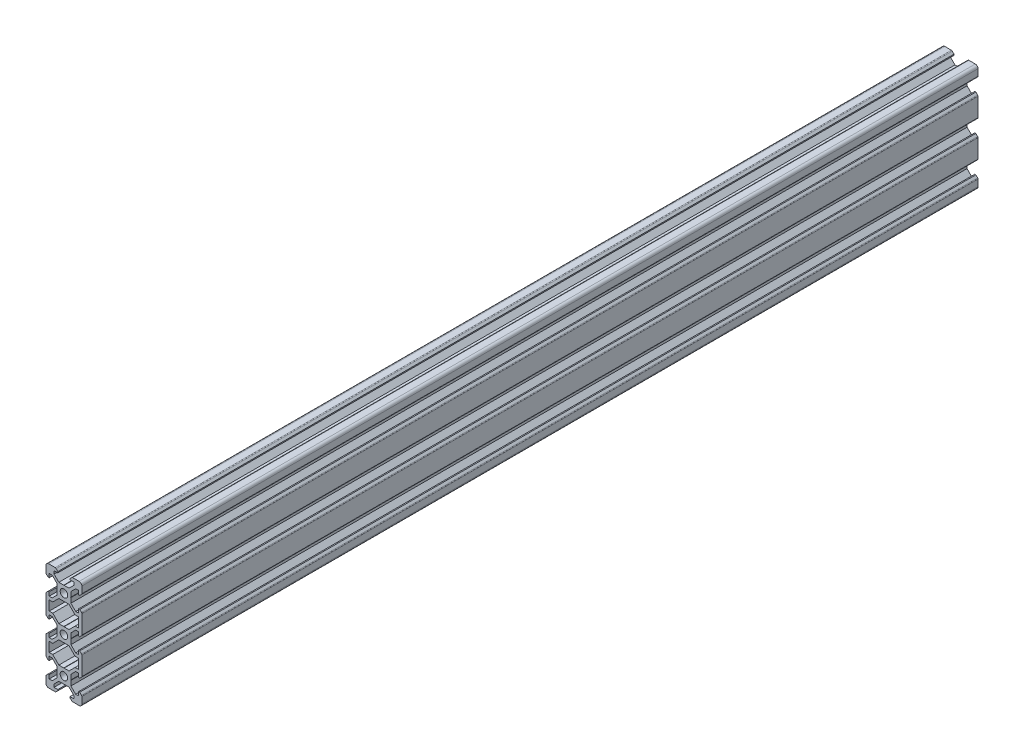
SolidWorks part; units mm, degrees
material "6063-T5"
ref_plane "Front" through (0, 0, 0) normal (0, 0, 1) x (1, 0, 0)
ref_plane "Top" through (0, 0, 0) normal (0, 1, 0) x (1, 0, 0)
ref_plane "Right" through (0, 0, 0) normal (1, 0, 0) x (0, 0, -1)
sketch "Sketch1" plane through (0, 0, 0) normal (0, 0, 1) x (1, 0, 0)
  line L0 (-8.5, 10) -> (-10, 8.5) construction
  line L1 (-8.5, 10) -> (-4.8628, 10)
  line L2 (-10, 8.5) -> (-10, 4.8628)
  line L3 (25.9287, -20) -> (-28.3599, -20) construction
  line L4 (10, 8.5) -> (10, 4.8628)
  line L5 (-10, 10) -> (10, -10) construction
  line L6 (-10, -10) -> (10, 10) construction
  line L7 (8.2, -5.5) -> (8.2, -3.3865)
  line L8 (-8.2, -5.5) -> (-8.2, -3.3865)
  line L9 (-5.5, 8.2) -> (-3.3865, 8.2)
  line L10 (-8.2, -12.7) -> (-8.2, -7.3)
  line L11 (-3.9005, 2.8395) -> (-6.561, 5.5)
  line L12 (-6.561, 5.5) -> (-8.2, 5.5)
  line L13 (-2.8395, -3.9005) -> (-0.1, -3.9005)
  line L14 (-3.9005, -2.8395) -> (-3.9005, -0.1)
  line L15 (-2.8395, 3.9005) -> (-0.1, 3.9005)
  line L16 (3.9005, -2.8395) -> (3.9005, -0.1)
  line L17 (-8.2, 3.3865) -> (-8.81, 3.3865)
  line L18 (-8.81, 3.3865) -> (-9.7976, 4.3741)
  line L19 (8.5, 10) -> (10, 8.5) construction
  line L20 (-2.8395, 3.9005) -> (-5.5, 6.561)
  line L21 (-5.5, 6.561) -> (-5.5, 8.2)
  line L22 (-3.3865, 8.2) -> (-3.3865, 8.81)
  line L23 (-3.3865, 8.81) -> (-4.3741, 9.7976)
  line L24 (0, 24.069) -> (0, -33.8154) construction
  line L25 (3.3865, 8.81) -> (4.3741, 9.7976)
  line L26 (3.3865, 8.2) -> (3.3865, 8.81)
  line L27 (5.5, 6.561) -> (5.5, 8.2)
  line L28 (2.8395, 3.9005) -> (5.5, 6.561)
  line L29 (3.3865, 8.2) -> (5.5, 8.2)
  line L30 (4.8628, 10) -> (8.5, 10)
  line L31 (-0.1, 3.9005) -> (0, 3.8005)
  line L32 (0.1, 3.9005) -> (0, 3.8005)
  line L33 (0.1, 3.9005) -> (2.8395, 3.9005)
  line L34 (25.9287, 0) -> (-28.3459, 0) construction
  line L35 (-0.1, -3.9005) -> (0, -3.8005)
  line L36 (0.1, -3.9005) -> (0, -3.8005)
  line L37 (0.1, -3.9005) -> (2.8395, -3.9005)
  line L38 (-3.9005, 0.1) -> (-3.8005, 0)
  line L39 (-3.8005, 0) -> (-3.9005, -0.1)
  line L40 (-3.9005, 0.1) -> (-3.9005, 2.8395)
  line L41 (3.9005, 0.1) -> (3.8005, 0)
  line L42 (3.8005, 0) -> (3.9005, -0.1)
  line L43 (3.9005, 0.1) -> (3.9005, 2.8395)
  line L44 (8.81, 3.3865) -> (9.7976, 4.3741)
  line L45 (8.2, 3.3865) -> (8.81, 3.3865)
  line L46 (6.561, 5.5) -> (8.2, 5.5)
  line L47 (3.9005, 2.8395) -> (6.561, 5.5)
  line L48 (2.8395, -3.9005) -> (5.5, -6.561)
  line L49 (3.9005, -2.8395) -> (6.561, -5.5)
  line L50 (-2.8395, -3.9005) -> (-5.5, -6.561)
  line L51 (-3.9005, -2.8395) -> (-6.561, -5.5)
  line L52 (6.561, -5.5) -> (8.2, -5.5)
  line L53 (-6.561, -5.5) -> (-8.2, -5.5)
  line L54 (-8.81, -3.3865) -> (-9.7976, -4.3741)
  line L55 (-8.2, -3.3865) -> (-8.81, -3.3865)
  line L56 (8.81, -3.3865) -> (9.7976, -4.3741)
  line L57 (8.2, -3.3865) -> (8.81, -3.3865)
  line L58 (8.2, 3.3865) -> (8.2, 5.5)
  line L59 (10, -4.8628) -> (10, -15.1372)
  line L60 (-8.2, 3.3865) -> (-8.2, 5.5)
  line L61 (-10, -4.8628) -> (-10, -15.1372)
  line L62 (-28.3459, -10) -> (-10, -10) construction
  line L63 (-3.9005, -20.1) -> (-3.9005, -22.8395)
  line L64 (-3.9005, -20.1) -> (-3.8005, -20)
  line L65 (-3.8005, -20) -> (-3.9005, -19.9)
  line L66 (3.9005, -20.1) -> (3.9005, -22.8395)
  line L67 (3.9005, -20.1) -> (3.8005, -20)
  line L68 (3.8005, -20) -> (3.9005, -19.9)
  line L69 (6.561, -14.5) -> (8.2, -14.5)
  line L70 (3.9005, -17.1605) -> (6.561, -14.5)
  line L71 (3.9005, -17.1605) -> (3.9005, -19.9)
  line L72 (-3.9005, -17.1605) -> (-3.9005, -19.9)
  line L73 (-3.9005, -17.1605) -> (-6.561, -14.5)
  line L74 (-6.561, -14.5) -> (-8.2, -14.5)
  line L75 (-8.2, -16.6135) -> (-8.81, -16.6135)
  line L76 (-8.81, -16.6135) -> (-9.7976, -15.6259)
  line L77 (8.2, -16.6135) -> (8.81, -16.6135)
  line L78 (8.81, -16.6135) -> (9.7976, -15.6259)
  line L79 (-2.8395, -16.0995) -> (-5.5, -13.439)
  line L80 (-2.8395, -16.0995) -> (-0.1, -16.0995)
  line L81 (-0.1, -16.0995) -> (0, -16.1995)
  line L82 (0.1, -16.0995) -> (0, -16.1995)
  line L83 (0.1, -16.0995) -> (2.8395, -16.0995)
  line L84 (2.8395, -16.0995) -> (5.5, -13.439)
  line L85 (-8.2, -16.6135) -> (-8.2, -14.5)
  line L86 (8.2, -16.6135) -> (8.2, -14.5)
  line L87 (2.8395, -23.9005) -> (5.5, -26.561)
  line L88 (-2.8395, -23.9005) -> (-5.5, -26.561)
  line L89 (-0.1, -23.9005) -> (0, -23.8005)
  line L90 (0.1, -23.9005) -> (0, -23.8005)
  line L91 (0.1, -23.9005) -> (2.8395, -23.9005)
  line L92 (-2.8395, -23.9005) -> (-0.1, -23.9005)
  line L93 (-8.2, -23.3865) -> (-8.2, -25.5)
  line L94 (-8.2, -23.3865) -> (-8.81, -23.3865)
  line L95 (-8.81, -23.3865) -> (-9.7976, -24.3741)
  line L96 (8.2, -23.3865) -> (8.2, -25.5)
  line L97 (8.2, -23.3865) -> (8.81, -23.3865)
  line L98 (8.81, -23.3865) -> (9.7976, -24.3741)
  line L99 (8.2, -27.3) -> (8.2, -32.7)
  line L100 (10, -35.1372) -> (10, -24.8628)
  line L101 (-10, -35.1372) -> (-10, -24.8628)
  line L102 (-8.2, -27.3) -> (-8.2, -32.7)
  line L103 (3.9005, -22.8395) -> (6.561, -25.5)
  line L104 (-3.9005, -22.8395) -> (-6.561, -25.5)
  line L105 (6.239, -27.3) -> (8.2, -27.3)
  line L106 (-6.239, -27.3) -> (-8.2, -27.3)
  line L107 (-6.561, -25.5) -> (-8.2, -25.5)
  line L108 (6.561, -25.5) -> (8.2, -25.5)
  line L109 (5.5, -26.561) -> (6.239, -27.3)
  line L110 (-5.5, -26.561) -> (-6.239, -27.3)
  line L111 (8.2, -34.5) -> (8.2, -36.6135)
  line L112 (8.2, -36.6135) -> (8.81, -36.6135)
  line L113 (8.81, -36.6135) -> (9.7976, -35.6259)
  line L114 (-8.2, -34.5) -> (-8.2, -36.6135)
  line L115 (-6.239, -7.3) -> (-8.2, -7.3)
  line L116 (-5.5, -6.561) -> (-6.239, -7.3)
  line L117 (6.239, -7.3) -> (8.2, -7.3)
  line L118 (5.5, -6.561) -> (6.239, -7.3)
  line L119 (-6.239, -12.7) -> (-8.2, -12.7)
  line L120 (-5.5, -13.439) -> (-6.239, -12.7)
  line L121 (5.5, -13.439) -> (6.239, -12.7)
  line L122 (6.239, -12.7) -> (8.2, -12.7)
  line L123 (8.2, -12.7) -> (8.2, -7.3)
  line L124 (-8.2, -36.6135) -> (-8.81, -36.6135)
  line L125 (10, -10) -> (25.9287, -10) construction
  line L126 (-8.81, -36.6135) -> (-9.7976, -35.6259)
  line L128 (-0.1, -36.0995) -> (0, -36.1995)
  line L129 (0.1, -36.0995) -> (0, -36.1995)
  line L130 (0.1, -36.0995) -> (2.8395, -36.0995)
  line L131 (-6.561, -34.5) -> (-8.2, -34.5)
  line L132 (6.561, -34.5) -> (8.2, -34.5)
  line L133 (6.239, -32.7) -> (8.2, -32.7)
  line L134 (-6.239, -32.7) -> (-8.2, -32.7)
  line L135 (-5.5, -33.439) -> (-6.239, -32.7)
  line L136 (5.5, -33.439) -> (6.239, -32.7)
  line L137 (-8.81, -43.3865) -> (-9.7976, -44.3741)
  line L138 (-8.2, -43.3865) -> (-8.81, -43.3865)
  line L139 (-8.2, -43.3865) -> (-8.2, -45.5)
  line L140 (-6.561, -45.5) -> (-8.2, -45.5)
  line L141 (-10, -48.5) -> (-10, -44.8628)
  line L142 (-8.5, -50) -> (-4.8628, -50)
  line L143 (-3.3865, -48.81) -> (-4.3741, -49.7976)
  line L144 (-3.3865, -48.2) -> (-3.3865, -48.81)
  line L145 (-5.5, -48.2) -> (-3.3865, -48.2)
  line L146 (-5.5, -46.561) -> (-5.5, -48.2)
  line L147 (3.3865, -48.2) -> (5.5, -48.2)
  line L148 (3.3865, -48.2) -> (3.3865, -48.81)
  line L149 (3.3865, -48.81) -> (4.3741, -49.7976)
  line L150 (4.8628, -50) -> (8.5, -50)
  line L151 (5.5, -46.561) -> (5.5, -48.2)
  line L152 (6.561, -45.5) -> (8.2, -45.5)
  line L153 (8.2, -43.3865) -> (8.2, -45.5)
  line L154 (10, -48.5) -> (10, -44.8628)
  line L155 (8.81, -43.3865) -> (9.7976, -44.3741)
  line L156 (8.2, -43.3865) -> (8.81, -43.3865)
  line L157 (-0.1, -43.9005) -> (0, -43.8005)
  line L158 (0.1, -43.9005) -> (0, -43.8005)
  line L159 (-2.8395, -43.9005) -> (-0.1, -43.9005)
  line L160 (0.1, -43.9005) -> (2.8395, -43.9005)
  line L161 (3.9005, -40.1) -> (3.8005, -40)
  line L162 (3.8005, -40) -> (3.9005, -39.9)
  line L163 (3.9005, -37.1605) -> (3.9005, -39.9)
  line L164 (3.9005, -40.1) -> (3.9005, -42.8395)
  line L165 (-2.8395, -36.0995) -> (-0.1, -36.0995)
  line L166 (-2.8395, -43.9005) -> (-5.5, -46.561)
  line L167 (-3.9005, -37.1605) -> (-3.9005, -39.9)
  line L168 (-3.8005, -40) -> (-3.9005, -39.9)
  line L169 (-3.9005, -40.1) -> (-3.8005, -40)
  line L170 (-3.9005, -42.8395) -> (-6.561, -45.5)
  line L171 (2.8395, -43.9005) -> (5.5, -46.561)
  line L172 (3.9005, -42.8395) -> (6.561, -45.5)
  line L173 (3.9005, -37.1605) -> (6.561, -34.5)
  line L174 (2.8395, -36.0995) -> (5.5, -33.439)
  line L175 (-3.9005, -42.8395) -> (-3.9005, -40.1)
  line L176 (-6.561, -34.5) -> (-3.9005, -37.1605)
  line L177 (-5.5, -33.439) -> (-2.8395, -36.0995)
  circle A0 centre (0, 0) radius 2.1
  arc A1 (-8.5, 10) -> (-10, 8.5) centre (-8.5, 8.5) ccw
  arc A2 (10, 8.5) -> (8.5, 10) centre (8.5, 8.5) ccw
  arc A3 (-4.3741, 9.7976) -> (-4.8628, 10) centre (-4.8628, 9.3088) ccw
  arc A4 (4.8628, 10) -> (4.3741, 9.7976) centre (4.8628, 9.3088) ccw
  circle A5 centre (0, -20) radius 2.1
  arc A6 (9.7976, 4.3741) -> (10, 4.8628) centre (9.3088, 4.8628) ccw
  arc A7 (-10, 4.8628) -> (-9.7976, 4.3741) centre (-9.3088, 4.8628) ccw
  arc A8 (-10, -4.8628) -> (-9.7976, -4.3741) centre (-9.3088, -4.8628) cw
  arc A9 (9.7976, -4.3741) -> (10, -4.8628) centre (9.3088, -4.8628) cw
  arc A10 (-10, -15.1372) -> (-9.7976, -15.6259) centre (-9.3088, -15.1372) ccw
  arc A11 (9.7976, -15.6259) -> (10, -15.1372) centre (9.3088, -15.1372) ccw
  arc A12 (-10, -24.8628) -> (-9.7976, -24.3741) centre (-9.3088, -24.8628) cw
  arc A13 (9.7976, -24.3741) -> (10, -24.8628) centre (9.3088, -24.8628) cw
  arc A14 (9.7976, -35.6259) -> (10, -35.1372) centre (9.3088, -35.1372) ccw
  arc A15 (-10, -35.1372) -> (-9.7976, -35.6259) centre (-9.3088, -35.1372) ccw
  circle A16 centre (0, -40) radius 2.1
  arc A17 (-10, -44.8628) -> (-9.7976, -44.3741) centre (-9.3088, -44.8628) cw
  arc A18 (-8.5, -50) -> (-10, -48.5) centre (-8.5, -48.5) cw
  arc A19 (-4.3741, -49.7976) -> (-4.8628, -50) centre (-4.8628, -49.3088) cw
  arc A20 (4.8628, -50) -> (4.3741, -49.7976) centre (4.8628, -49.3088) cw
  arc A21 (10, -48.5) -> (8.5, -50) centre (8.5, -48.5) cw
  arc A22 (9.7976, -44.3741) -> (10, -44.8628) centre (9.3088, -44.8628) cw
  point P17 (-9.25, 9.25)
  point P21 (9.25, 9.25)
  dimension "D2" = 4.2
  dimension "D4" = 1.5
  dimension "D3" = 20
  dimension "D5" = 0.529
  dimension "D6" = 6.773
  dimension "D7" = 90
  dimension "D8" = 11
  dimension "D9" = 0.61
  dimension "D10" = 0.1
  dimension "D11" = 0.1
  dimension "D12" = 0.1
  dimension "D13" = 0.1
  dimension "D14" = 5.679
  dimension "D15" = 1.639
  dimension "D16" = 1.8
  dimension "D17" = 90
  dimension "D18" = 6.773
  dimension "D19" = 90
  dimension "D20" = 20
  dimension "D21" = 1.8
extrude "Boss-Extrude2" add sketch "Sketch1" along normal blind 500
